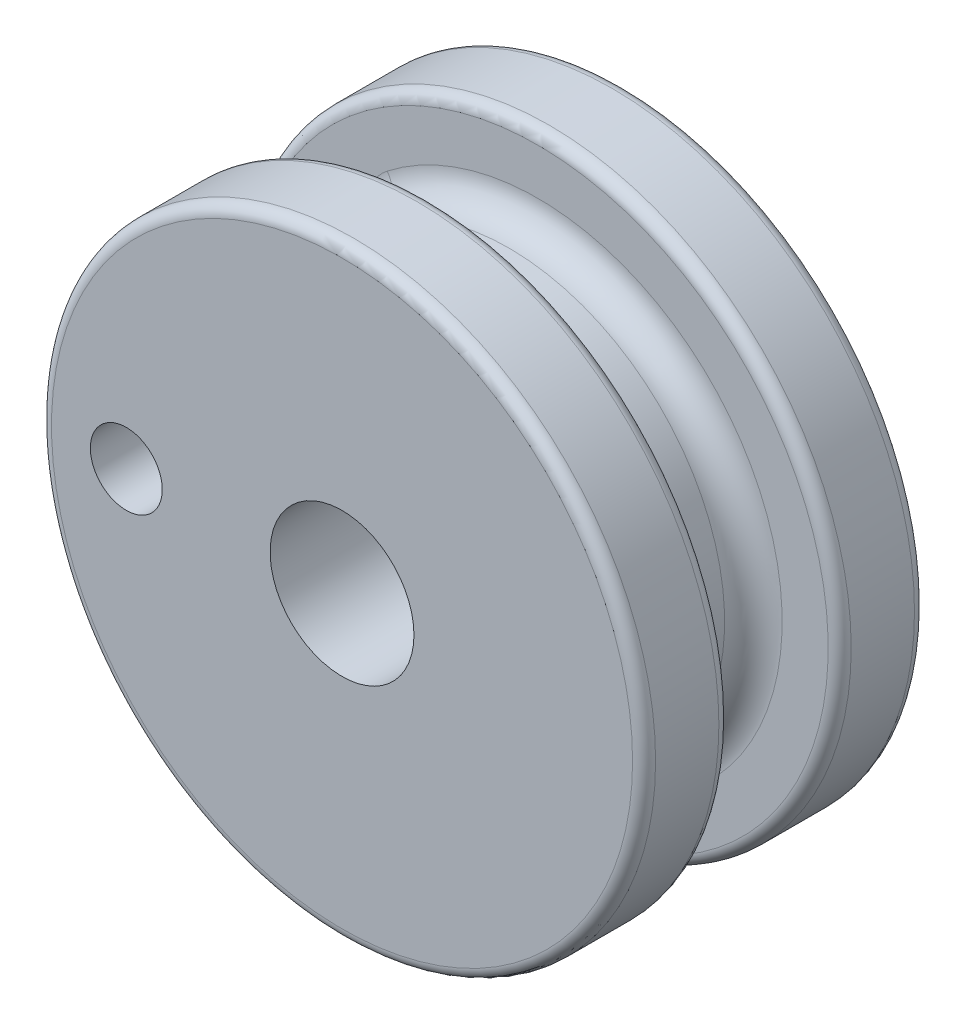
SolidWorks part; units mm, degrees
ref_plane "Front Plane" through (0, 0, 0) normal (0, 0, 1) x (1, 0, 0)
ref_plane "Top Plane" through (0, 0, 0) normal (0, 1, 0) x (1, 0, 0)
ref_plane "Right Plane" through (0, 0, 0) normal (1, 0, 0) x (0, 0, -1)
ref_plane "Plane1" through (0, 0, -15.24) normal (0, 0, 1) x (1, 0, 0)
sketch "Sketch1" plane through (0, 0, 0) normal (0, 0, 1) x (1, 0, 0)
  line L4 (-29.9247, -0.635) -> (-29.9247, 0.635)
  line L5 (-29.9247, -0.635) -> (-29.9247, 0.635) construction
  line L6 (-35.0047, 5.715) -> (-51.5147, 5.715)
  line L7 (-35.0047, 5.715) -> (-51.5147, 5.715) construction
  line L8 (-51.5147, 5.715) -> (-51.5147, -5.715)
  line L9 (-51.5147, 5.715) -> (-51.5147, -5.715) construction
  line L92 (-51.5147, -5.715) -> (-35.0047, -5.715)
  line L93 (-51.5147, -5.715) -> (-35.0047, -5.715)
  circle A0 centre (-38.1797, 0) radius 3.175 construction
  circle A1 centre (-38.1797, 0) radius 3.175
  arc A2 (-35.0047, -5.715) -> (-29.9247, -0.635) centre (-35.0047, -0.635) ccw
  arc A3 (-35.0047, -5.715) -> (-29.9247, -0.635) centre (-35.0047, -0.635) ccw construction
  arc A4 (-29.9247, 0.635) -> (-35.0047, 5.715) centre (-35.0047, 0.635) ccw
  arc A5 (-29.9247, 0.635) -> (-35.0047, 5.715) centre (-35.0047, 0.635) ccw construction
  circle A6 centre (-38.1797, 0) radius 9.525
  circle A7 centre (-38.1797, 0) radius 13.335 construction
  dimension "D2" = 19.05
  dimension "D3" = 3.81
  dimension "D1" = 0
extrude "Boss-Extrude1" add sketch "Sketch1" along normal mid plane 12.446 from surface at -15.24 starting at plane "Plane1"
sketch "Sketch3" plane through (0, 0, -9.017) normal (0, 0, 1) x (1, 0, 0)
  circle A0 centre (-38.1797, 0) radius 13.335 construction
  circle A1 centre (-38.1797, 0) radius 13.335
  circle A3 centre (-38.1797, 0) radius 3.175 construction
  circle A4 centre (-38.1797, 0) radius 3.175
extrude "Boss-Extrude2" add sketch "Sketch3" against normal blind 3.81
mirror "Mirror1" about plane through (0, 0, -15.24) normal (0, 0, 1) of "Boss-Extrude2"
hole_wizard "1/8 (0.1250) Dowel Hole1" positions "Sketch4" profile "Sketch5" hole size "1/8" standard "ANSI Inch" end condition through all
sketch "Sketch4" plane through (0, 0, -21.463) normal (0, 0, 1) x (1, 0, 0)
  line L1 (-38.1797, 0) -> (-29.6082, -10.2152) construction
  line L3 (-38.1797, 0) -> (-35.8641, 13.1324) construction
  line L7 (-38.1797, 0) -> (-24.8447, 0) construction
  circle A2 centre (-38.1797, 0) radius 13.335 construction
  circle A3 centre (-38.1797, 0) radius 9.525 construction
  point P41 (-47.7047, 0)
  dimension "D1" = 50
  dimension "D2" = 80
sketch "Sketch5" plane through (-47.7047, 0, -21.463) normal (1, 0, 0) x (0, 1, 0)
  line L0 (0, 0) -> (0, 12.446)
  line L1 (0, 12.446) -> (1.5875, 12.446)
  line L2 (1.5875, 12.446) -> (1.5875, 0)
  line L5 (1.5875, 0) -> (0, 0)
  line L11 (0, -6.35) -> (0, 107.95) construction
  dimension "Thru Hole Dia." = 3.175
  dimension "Thru Hole Depth" = 12.446
sketch "Sketch9" plane through (0, 0, -15.24) normal (0, 0, 1) x (1, 0, 0)
  line L1 (-44.5297, 7.0995) -> (-50.8797, 7.0995)
  line L2 (-44.5297, 7.0995) -> (-44.5297, -7.0995)
  line L3 (-44.5297, -7.0995) -> (-50.8797, -7.0995)
  line L4 (-50.8797, 7.0995) -> (-50.8797, -7.0995)
  line L5 (-44.5297, 7.0995) -> (-50.8797, -7.0995) construction
  line L6 (-44.5297, -7.0995) -> (-50.8797, 7.0995) construction
  circle A0 centre (-47.7047, 0) radius 1.5875 construction
  circle A2 centre (-38.1797, 0) radius 9.525 construction
  point P0 (-47.7047, 0)
  dimension "D1" = 6.35
extrude "Cut-Extrude2" cut sketch "Sketch9" against normal up to surface and the other way up to surface up to face at (-24.8447, 0, -17.653) other way up to face at (-24.8447, 0, -12.827)
fillet "Fillet2" radius 1.27 6 edges at (-28.6547, 0, -17.653) (-28.6547, 0, -12.827) (-44.5297, 0, -12.827) (-44.5297, 0, -17.653) (-44.5297, -7.0995, -15.24) (-44.5297, 7.0995, -15.24)
fillet "Fillet3" radius 0.508 4 edges at (-24.8447, 0, -12.827) (-24.8447, 0, -9.017) (-24.8447, 0, -17.653) (-24.8447, 0, -21.463)
